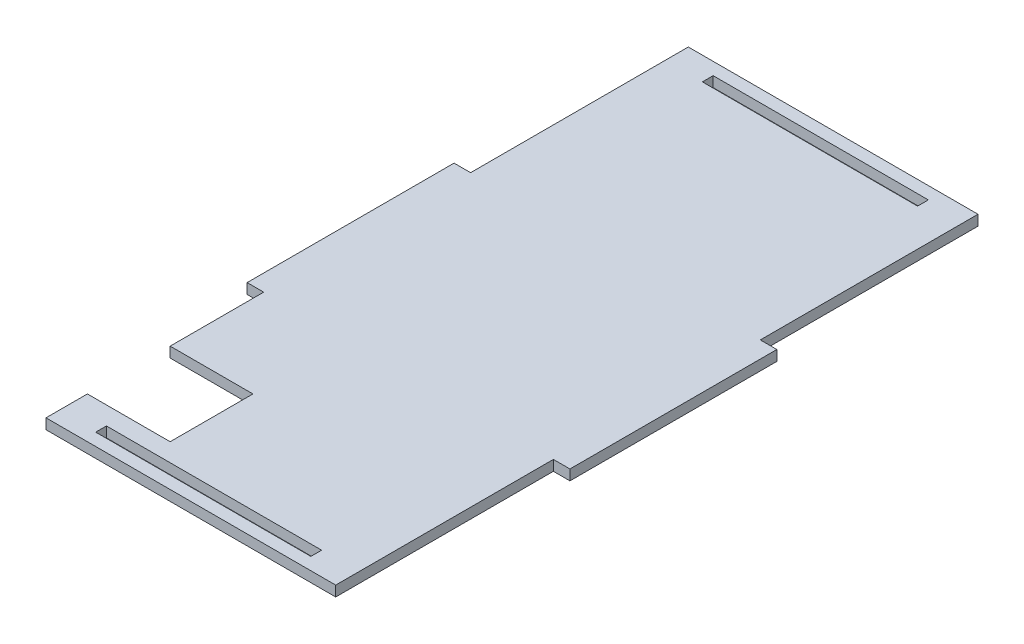
SolidWorks part; units mm, degrees
ref_plane "Front Plane" through (0, 0, 0) normal (0, 0, 1) x (1, 0, 0)
ref_plane "Top Plane" through (0, 0, 0) normal (0, 1, 0) x (1, 0, 0)
ref_plane "Right Plane" through (0, 0, 0) normal (1, 0, 0) x (0, 0, -1)
sketch "Sketch2" plane through (0, 0, 0) normal (0, 1, 0) x (1, 0, 0)
  line L7 (35, 25) -> (35, 77.6)
  line L8 (35, 77.6) -> (-35, 77.6)
  line L9 (-35, 77.6) -> (-35, 25)
  line L10 (-35, 25) -> (-39, 25)
  line L11 (-39, 25) -> (-39, -25)
  line L16 (26, 74.6) -> (26, 72)
  line L17 (-26, 72) -> (26, 72)
  line L18 (-26, 74.6) -> (-26, 72)
  line L19 (-26, 74.6) -> (26, 74.6)
  line L20 (-112.7216, 0) -> (112.7216, 0) construction
  line L21 (0, -85.5857) -> (0, 85.5857) construction
  line L22 (35, -25) -> (35, -77.6)
  line L23 (-26, -74.6) -> (26, -74.6)
  line L24 (-26, -74.6) -> (-26, -72)
  line L25 (-26, -72) -> (26, -72)
  line L26 (26, -74.6) -> (26, -72)
  line L27 (35, -77.6) -> (-35, -77.6)
  line L28 (-35, -77.6) -> (-35, -67.6)
  line L29 (-35, -25) -> (-39, -25)
  line L30 (35, -25) -> (39, -25)
  line L31 (35, 25) -> (39, 25)
  line L32 (39, 25) -> (39, -25)
  line L33 (-35, -47.6) -> (-15, -47.6)
  line L34 (-15, -47.6) -> (-15, -67.6)
  line L35 (-15, -67.6) -> (-35, -67.6)
  line L36 (-35, -47.6) -> (-35, -25)
  point P0 (-39, 0)
  point P2 (0, 77.6)
  point P24 (0, 0)
  point P28 (0, 0)
  dimension "D1" = 4
  dimension "D2" = 25
  dimension "D3" = 52
  dimension "D4" = 2.6
  dimension "D5" = 26
  dimension "D6" = 2.6
  dimension "D7" = 20
  dimension "D8" = 3
  dimension "D9" = 70
  dimension "D10" = 35
  dimension "D11" = 72
  dimension "D12" = 20
  dimension "D13" = 10
extrude "Boss-Extrude1" add sketch "Sketch2" along normal blind 2.5
